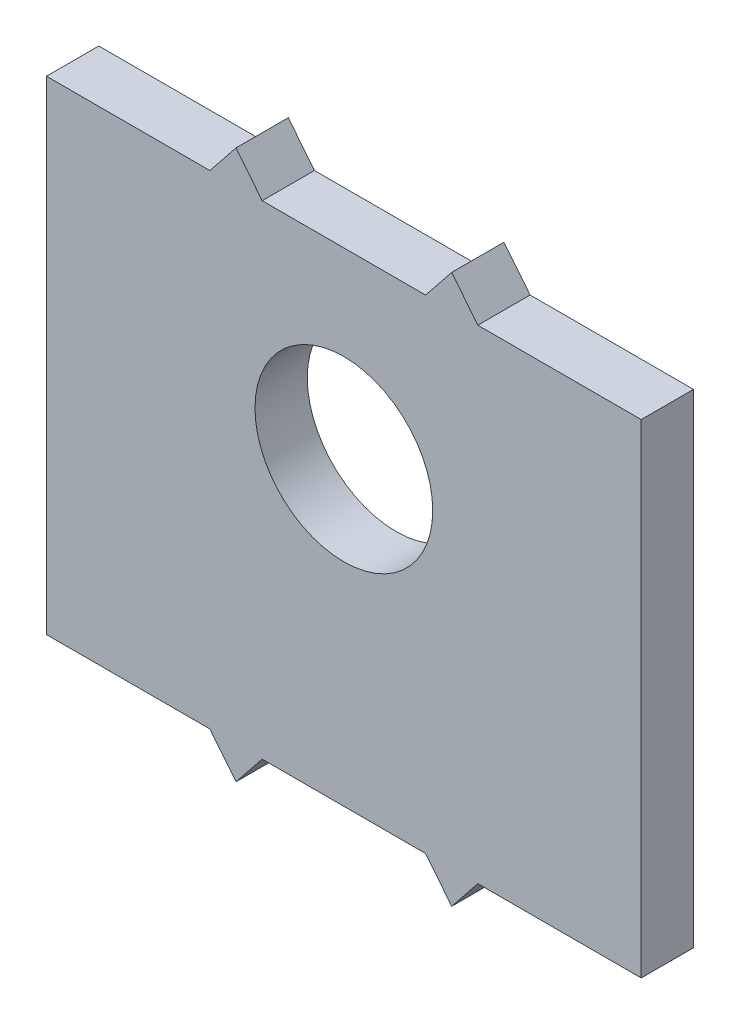
SolidWorks part; units mm, degrees
ref_plane "Front Plane" through (0, 0, 0) normal (0, 0, 1) x (1, 0, 0)
ref_plane "Top Plane" through (0, 0, 0) normal (0, 1, 0) x (1, 0, 0)
ref_plane "Right Plane" through (0, 0, 0) normal (1, 0, 0) x (0, 0, -1)
sketch "Sketch1" plane through (0, 0, 0) normal (0, 0, 1) x (1, 0, 0)
  line L0 (22.75, 37) -> (22.75, 14.7203) construction
  line L1 (0, 0) -> (45.5, 0)
  line L2 (0, 0) -> (0, 37)
  line L3 (0, 37) -> (45.5, 37)
  line L4 (45.5, 0) -> (45.5, 37)
  line L5 (12.5, 37) -> (14.5, 39.5)
  line L6 (14.5, 39.5) -> (16.5, 37)
  line L7 (31, 39.5) -> (29, 37)
  line L8 (33, 37) -> (31, 39.5)
  line L9 (0, 18.5) -> (57.9593, 18.5) construction
  line L10 (33, 0) -> (31, -2.5)
  line L11 (31, -2.5) -> (29, 0)
  line L12 (14.5, -2.5) -> (16.5, 0)
  line L13 (12.5, 0) -> (14.5, -2.5)
  point P9 (22.75, 37)
  point P16 (0, 18.5)
  point P17 (32, 38.25)
  point P18 (32, -1.25)
  dimension "D1" = 37
  dimension "D2" = 45.5
  dimension "D3" = 16.5
  dimension "D4" = 2.5
  dimension "D5" = 4
extrude "Basis" add sketch "Sketch1" along normal blind 4 contours L1 L4 L3 L2 | L6 L5 L3 | L3 L8 L7 | L1 L13 L12 | L11 L10 L1
sketch "Sketch2" plane through (0, 0, 4) normal (0, 0, 1) x (1, 0, 0)
  line L0 (16.5, 37) -> (29, 37) construction
  circle A0 centre (22.75, 23) radius 6.8
  point P5 (22.75, 37)
  dimension "D1" = 13.6
  dimension "D2" = 14
extrude "Camera gat " cut sketch "Sketch2" against normal up to surface (4 mm away) up to face at (22.75, 18.5, 0)
sketch "Sketch3" [suppressed] plane through (0, 0, 4) normal (0, 0, 1) x (1, 0, 0)
  line L0 (22.75, 37) -> (22.75, 0) construction
  line L1 (16.5, 37) -> (29, 37) construction
  line L2 (16.5, 0) -> (29, 0) construction
  line L3 (0, 37) -> (12.5, 37) construction
  circle A0 centre (9.8, 25.6) radius 7.95
  circle A1 centre (35.7, 25.6) radius 7.95
  dimension "D3" = 15.9
  dimension "D1" = 11.4
  dimension "D2" = 25.9
extrude "HR04 gat " [suppressed] cut sketch "Sketch3" against normal up to surface (4 mm away)
sketch "Sketch4" [suppressed] plane through (0, 0, 4) normal (0, 0, 1) x (1, 0, 0)
  line L0 (7.7992, 12.9938) -> (37.7008, 12.9938) construction
  line L1 (16.5, 37) -> (29, 37) construction
  text T0 "AFSTAND SENSOR" font "Yu Gothic UI Semilight" height 3.5
  point P5 (22.75, 12.9938)
  point P8 (22.75, 37)
extrude "Afstand sensor" [suppressed] cut sketch "Sketch4" against normal blind 0.2
sketch "Sketch6" [suppressed] plane through (0, 0, 4) normal (0, 0, 1) x (1, 0, 0)
  line L4 (16.5, 37) -> (29, 37) construction
  point P0 (22.75, 31.8)
  point P3 (22.75, 37)
  line B0 (9.1, 31.8) -> (36.4, 31.8)
  line B1 (9.1, 31.8) -> (9.1, 16.3191)
  line B2 (9.1, 16.3191) -> (36.4, 16.3191)
  line B3 (36.4, 31.8) -> (36.4, 16.3191)
  circle B4 centre (11.1, 34.0981) radius 1.5
  circle B5 centre (34.4, 34.0981) radius 1.5
  circle B6 centre (34.4, 10.2981) radius 1.5
  circle B7 centre (11.1, 10.2981) radius 1.5
  dimension "D1" = 5.2
sketch_block_instance "Block1-1" [suppressed]
sketch_block "Block1" parameters "D1"=3, "D2"=3, "D3"=3, "D4"=3
extrude "Cut-Extrude5" [suppressed] cut sketch "Sketch6" against normal up to surface (4 mm away)
sketch "Sketch7" [suppressed] plane through (0, 0, 4) normal (0, 0, 1) x (1, 0, 0)
  line L0 (-2.0092, 11.0348) -> (47.5092, 11.0348) construction
  line L1 (16.5, 37) -> (29, 37) construction
  text T0 "oled scherm " font "Yu Gothic UI Semilight" height 3.5
  point P4 (22.75, 37)
  point P5 (22.75, 11.0348)
extrude "Cut-Extrude6" [suppressed] cut sketch "Sketch7" against normal blind 0.2
sketch "Sketch9" [suppressed] plane through (0, 0, 4) normal (0, 0, 1) x (1, 0, 0)
  line L0 (15.4564, 12.6867) -> (24.4394, 12.6867) construction
  text T0 "V0.2"
